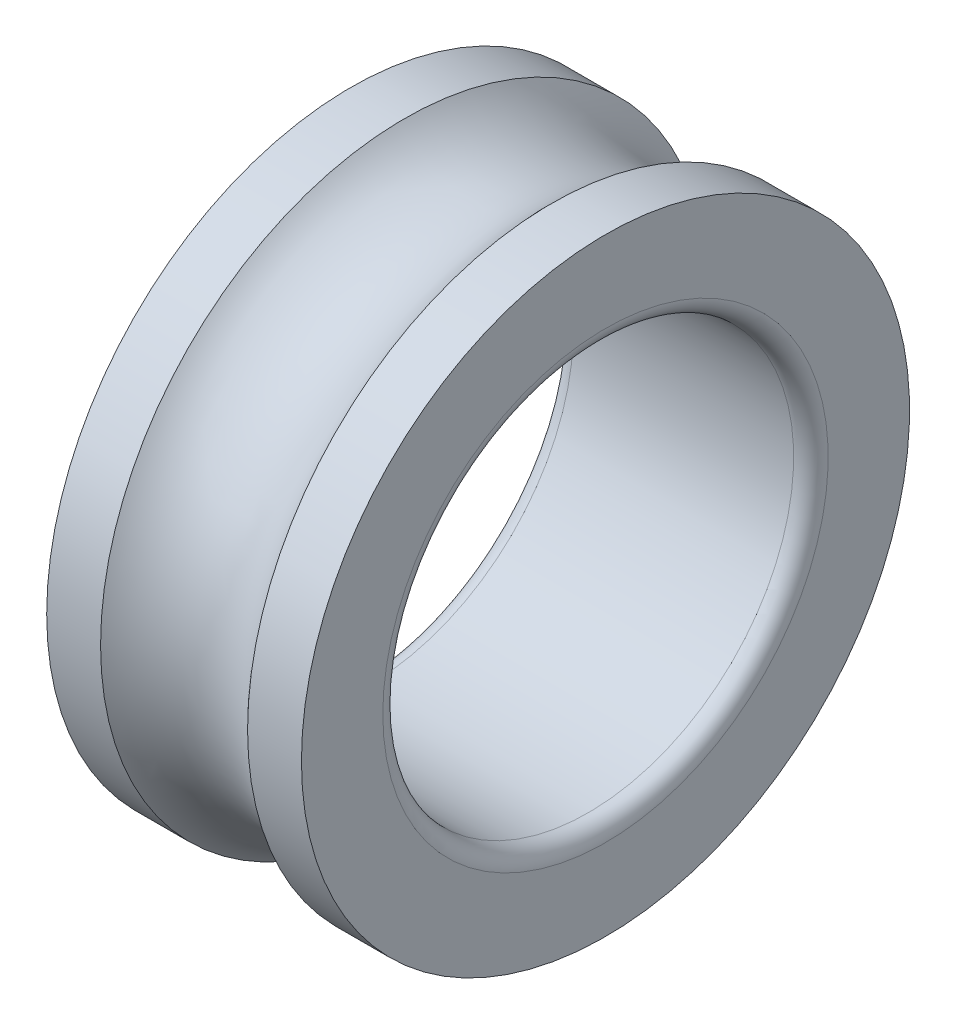
SolidWorks part; units mm, degrees
ref_plane "Front Plane" through (0, 0, 0) normal (0, 0, 1) x (1, 0, 0)
ref_plane "Top Plane" through (0, 0, 0) normal (0, 1, 0) x (1, 0, 0)
ref_plane "Right Plane" through (0, 0, 0) normal (1, 0, 0) x (0, 0, -1)
sketch "Sketch2" plane through (0, 0, 0) normal (0, 1, 0) x (1, 0, 0)
  line L0 (-586.613, 0) -> (1141.73, 0) construction
  line L1 (0, 635) -> (0, 0) construction
  line L2 (-340.36, 635) -> (340.36, 635)
  line L3 (-393.7, 688.34) -> (-393.7, 939.8)
  line L4 (-393.7, 939.8) -> (-227.1845, 939.8)
  line L5 (393.7, 688.34) -> (393.7, 939.8)
  line L6 (-393.7, 635) -> (393.7, 939.8) construction
  line L7 (-393.7, 939.8) -> (393.7, 635) construction
  line L8 (227.1845, 939.8) -> (393.7, 939.8)
  arc A0 (-227.1845, 939.8) -> (227.1845, 939.8) centre (0, 1143) ccw
  arc A1 (340.36, 635) -> (393.7, 688.34) centre (340.36, 688.34) ccw
  arc A2 (-340.36, 635) -> (-393.7, 688.34) centre (-340.36, 688.34) cw
  point P3 (0, 787.4)
  dimension "D5" = 304.8
  dimension "D6" = 53.34
  dimension "D1" = 787.4
  dimension "D2" = 635
  dimension "D3" = 939.8
  dimension "D4" = 203.2
revolve "Revolve1" add sketch "Sketch2" angle 360 about L0
